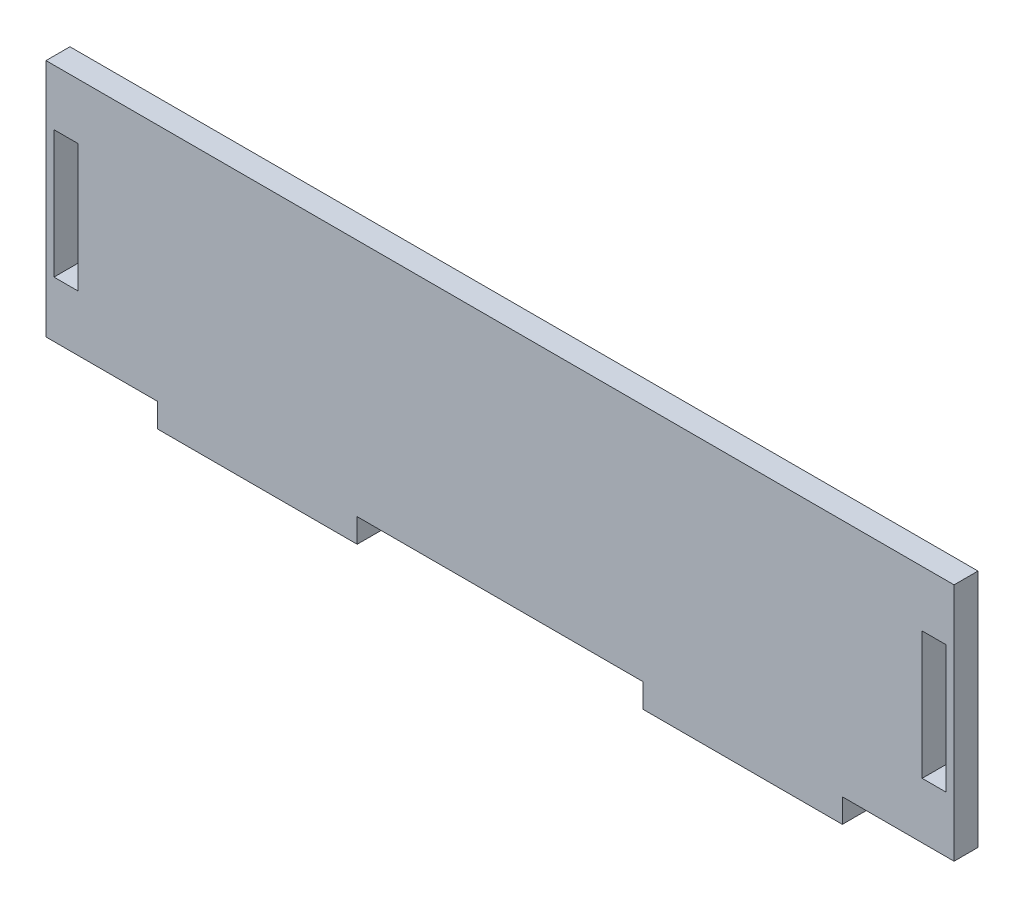
SolidWorks part; units mm, degrees
ref_plane "前视基准面" through (0, 0, 0) normal (0, 0, 1) x (1, 0, 0)
ref_plane "上视基准面" through (0, 0, 0) normal (0, 1, 0) x (1, 0, 0)
ref_plane "右视基准面" through (0, 0, 0) normal (1, 0, 0) x (0, 0, -1)
sketch "草图2" plane through (0, 0, 0) normal (0, 0, 1) x (1, 0, 0)
  line L0 (59.4, 0) -> (77.3, 0)
  line L1 (2.5, 0) -> (16.5, 0)
  line L3 (6.5, 30) -> (112.3, 30)
  line L5 (59.4, 0) -> (41.5, 0)
  line L7 (77.3, 0) -> (77.3, -3)
  line L8 (77.3, -3) -> (102.3, -3)
  line L9 (102.3, 0) -> (102.3, -3)
  line L10 (102.3, 0) -> (112.3, 0)
  line L12 (41.5, 0) -> (41.5, -3)
  line L13 (41.5, -3) -> (16.5, -3)
  line L14 (16.5, 0) -> (16.5, -3)
  line L39 (41.5, 0) -> (77.3, 0)
  line L40 (6.5, 23) -> (6.5, 30)
  line L45 (6.5, 7) -> (3.5, 7)
  line L46 (102.3, 0) -> (112.3, 0)
  line L51 (16.5, 0) -> (6.5, 0)
  line L52 (59.4, 0) -> (41.5, 0)
  line L53 (59.4, 0) -> (77.3, 0)
  line L54 (6.5, 7) -> (6.5, 23)
  line L55 (6.5, 23) -> (3.5, 23)
  line L56 (3.5, 7) -> (3.5, 23)
  line L57 (6.5, 30) -> (2.5, 30)
  line L58 (2.5, 30) -> (2.5, 0)
  line L59 (112.3, 7) -> (112.3, 30)
  line L61 (112.3, 15) -> (112.3, 7)
  line L65 (112.3, 15) -> (112.3, 23)
  line L69 (112.3, 30) -> (112.3, 7)
  line L72 (112.3, 30) -> (116.3, 30)
  line L73 (112.3, 23) -> (115.3, 23)
  line L74 (112.3, 23) -> (112.3, 7)
  line L75 (112.3, 7) -> (115.3, 7)
  line L76 (115.3, 23) -> (115.3, 7)
  line L77 (116.3, 30) -> (116.3, 0)
  line L78 (116.3, 0) -> (112.3, 0)
extrude "凸台-拉伸1" add sketch "草图2" along normal blind 3
